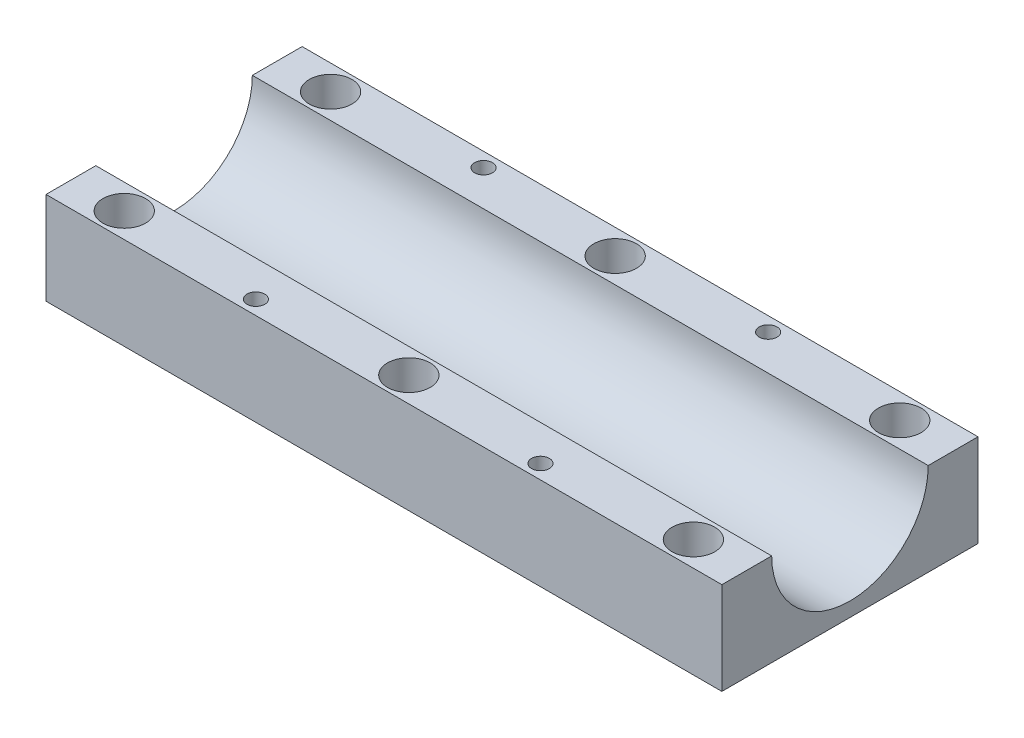
SolidWorks part; units mm, degrees
ref_plane "Спереди" through (0, 0, 0) normal (0, 0, 1) x (1, 0, 0)
ref_plane "Сверху" through (0, 0, 0) normal (0, 1, 0) x (1, 0, 0)
ref_plane "Справа" through (0, 0, 0) normal (1, 0, 0) x (0, 0, -1)
sketch "Эскиз1" plane through (0, 0, 0) normal (0, 1, 0) x (1, 0, 0)
  line L0 (0, 18) -> (95, 18) construction
  line L1 (0, 0) -> (95, 0)
  line L2 (0, 0) -> (0, 36)
  line L3 (0, 36) -> (95, 36)
  line L4 (95, 0) -> (95, 36)
  line L5 (0, 18) -> (0, 29) construction
  line L6 (0, 18) -> (0, 7) construction
  line L7 (0, 7) -> (95, 7) construction
  line L8 (95, 7) -> (95, 29) construction
  line L9 (95, 29) -> (0, 29) construction
  line L10 (0, 36) -> (0, 31) construction
  line L11 (95, 33) -> (95, 36) construction
  circle A0 centre (7.5, 32.5) radius 1.75
  circle A1 centre (47.5, 32.5) radius 1.75
  circle A2 centre (87.5, 32.5) radius 1.75
  circle A3 centre (87.5, 3.5) radius 1.75
  circle A4 centre (47.5, 3.5) radius 1.75
  circle A5 centre (7.5, 3.5) radius 1.75
  dimension "D5" = 3
  dimension "D1" = 95
  dimension "D2" = 36
  dimension "D3" = 22
  dimension "D4" = 7
  dimension "D6" = 40
  dimension "D7" = 3.5
  dimension "D8" = 7.5
extrude "Бобышка-Вытянуть1" add sketch "Эскиз1" along normal blind 13
sketch "Эскиз2" plane through (95, 0, 0) normal (1, 0, 0) x (0, 0, -1)
  line L0 (0, 13) -> (36, 13) construction
  circle A0 centre (18, 13) radius 11
extrude "Вырез-Вытянуть1" cut sketch "Эскиз2" against normal through all
sketch "Эскиз4" plane through (0, 13, 0) normal (0, 1, 0) x (1, 0, 0)
  line L0 (7.5, 32.5) -> (47.5, 32.5) construction
  line L1 (0, 18) -> (95, 18) construction
  line L2 (0, 29) -> (0, 7) construction
  line L3 (95, 7) -> (95, 29) construction
  line L5 (0, 36) -> (0, 29) construction
  line L6 (27.5, 32.5) -> (27.5, 34) construction
  line L7 (95, 36) -> (0, 36) construction
  circle A0 centre (7.5, 32.5) radius 3
  circle A1 centre (47.5, 32.5) radius 3
  circle A2 centre (87.5, 32.5) radius 3
  circle A10 centre (87.5, 3.5) radius 3
  circle A11 centre (47.5, 3.5) radius 3
  circle A12 centre (7.5, 3.5) radius 3
  circle A13 centre (27.5, 34) radius 1.25
  circle A14 centre (67.5, 34) radius 1.25
  circle A15 centre (67.5, 2) radius 1.25
  circle A16 centre (27.5, 2) radius 1.25
  dimension "D1" = 3
  dimension "D3" = 2
  dimension "D6" = 2.5
  dimension "D7" = 6
  dimension "D4" = 27.5
  dimension "D5" = 2
  dimension "D2" = 1
extrude "Вырез-Вытянуть2" cut sketch "Эскиз4" against normal blind 5
